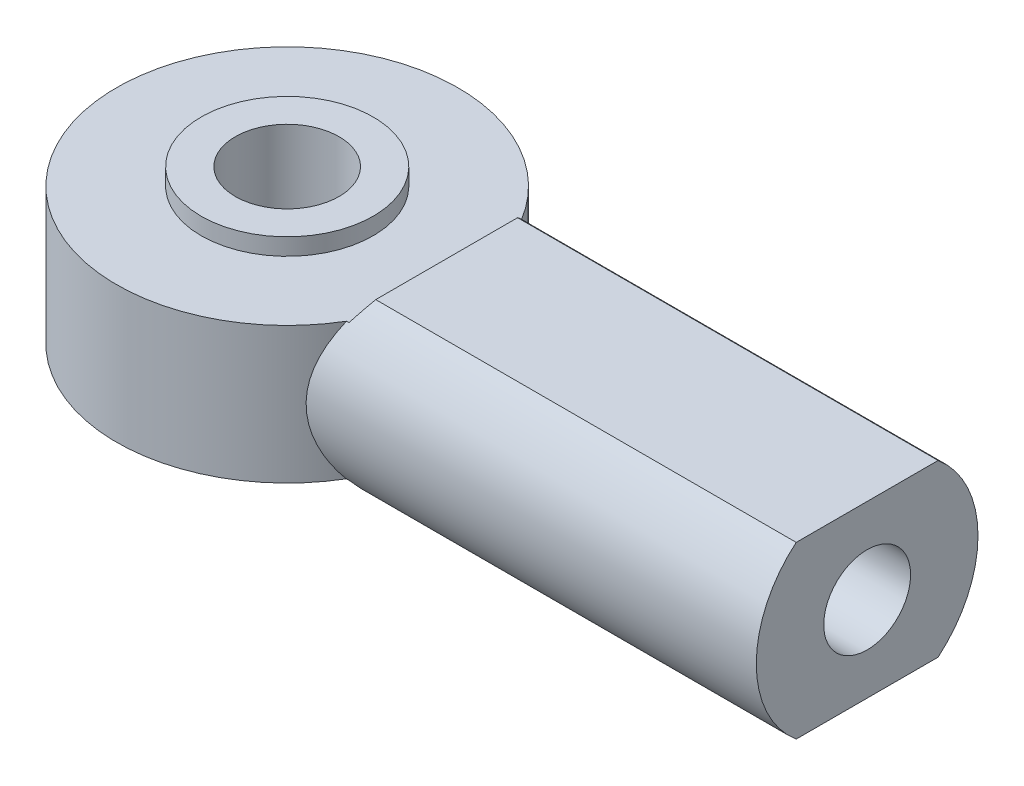
SolidWorks part; units mm, degrees
ref_plane "Front Plane" through (0, 0, 0) normal (0, 0, 1) x (1, 0, 0)
ref_plane "Top Plane" through (0, 0, 0) normal (0, 1, 0) x (1, 0, 0)
ref_plane "Right Plane" through (0, 0, 0) normal (1, 0, 0) x (0, 0, -1)
sketch "Sketch1" plane through (0, 0, 0) normal (0, 1, 0) x (1, 0, 0)
  circle A0 centre (0, 0) radius 7.9375
  dimension "D1" = 15.875
extrude "Head Diameter" add sketch "Sketch1" along normal mid plane 6.35
sketch "Sketch7" plane through (0, 0, 0) normal (1, 0, 0) x (0, 0, -1)
  line L1 (-3.2994, -3.9624) -> (3.2994, -3.9624)
  line L3 (-3.2994, 3.9624) -> (3.2994, 3.9624)
  arc A0 (-3.2994, 3.9624) -> (-3.2994, -3.9624) centre (0, 0) ccw
  arc A1 (3.2994, -3.9624) -> (3.2994, 3.9624) centre (0, 0) ccw
  point P0 (0, 0)
  point P1 (0, 3.9624)
  point P2 (0, -3.9624)
  point P3 (-5.1562, 0)
  point P4 (5.1562, 0)
  dimension "D2" = 5.1562
  dimension "D1" = 7.9248
extrude "Boss-Extrude4" add sketch "Sketch7" along normal blind 26.9748
sketch "Sketch8" plane through (0, 0, 0) normal (0, 0, 1) x (1, 0, 0)
  line L0 (0, 3.9624) -> (0, 3.175)
  line L1 (-7.9375, 3.175) -> (-7.9375, -3.175) construction
  line L2 (0, 3.175) -> (6.9342, 3.175)
  line L3 (6.9342, 3.175) -> (7.4168, 3.9624)
  line L4 (7.4168, 3.9624) -> (0, 3.9624)
  line L5 (-7.9375, 0) -> (7.4178, 0) construction
  line L6 (7.4168, -3.9624) -> (0, -3.9624)
  line L7 (6.9342, -3.175) -> (7.4168, -3.9624)
  line L8 (0, -3.175) -> (6.9342, -3.175)
  line L9 (0, -3.9624) -> (0, -3.175)
  dimension "D1" = 6.9342
  dimension "D2" = 7.4168
extrude "Cut-Extrude2" cut sketch "Sketch8" against normal mid plane 15.875
sketch "Sketch9" plane through (0, 0, 0) normal (0, 1, 0) x (1, 0, 0)
  circle A0 centre (0, 0) radius 4.0005
  dimension "D1" = 8.001
extrude "Boss-Extrude5" add sketch "Sketch9" along normal mid plane 7.9248
sketch "Sketch10" plane through (0, 3.9624, 0) normal (0, 1, 0) x (1, 0, 0)
  circle A0 centre (0, 0) radius 2.413
  dimension "D1" = 4.826
extrude "Cut-Extrude3" cut sketch "Sketch10" against normal blind 7.9248
sketch "Sketch18" plane through (26.9748, 0, 0) normal (1, 0, 0) x (0, 0, -1)
  point P0 (0, 0)
hole_wizard "#10-32 Tapped Hole1" positions "Sketch20" profile "Sketch19" tap size "#10-32" standard "Ansi Inch"
sketch "Sketch20" plane through (26.9748, 0, 0) normal (1, 0, 0) x (0, 0, -1)
  point P0 (0, 0)
sketch "Sketch19" plane through (26.9748, 0, 0) normal (0, 1, 0) x (0, 0, -1)
  line L0 (0, 0) -> (0, 15.4373)
  line L1 (0, 15.4373) -> (2.0193, 14.224)
  line L2 (2.0193, 14.224) -> (2.0193, 0)
  line L5 (2.0193, 0) -> (0, 0)
  line L10 (0, 15.4373) -> (-2.0193, 14.224) construction
  line L11 (0, -6.35) -> (0, 107.95) construction
  dimension "Tap Drill Dia." = 4.0386
  dimension "Tap Drill Depth" = 14.224
  dimension "Drill Angle" = 118
cosmetic thread "Hole Thread1" parameters "D1"=9.652, "D2"=4.826
